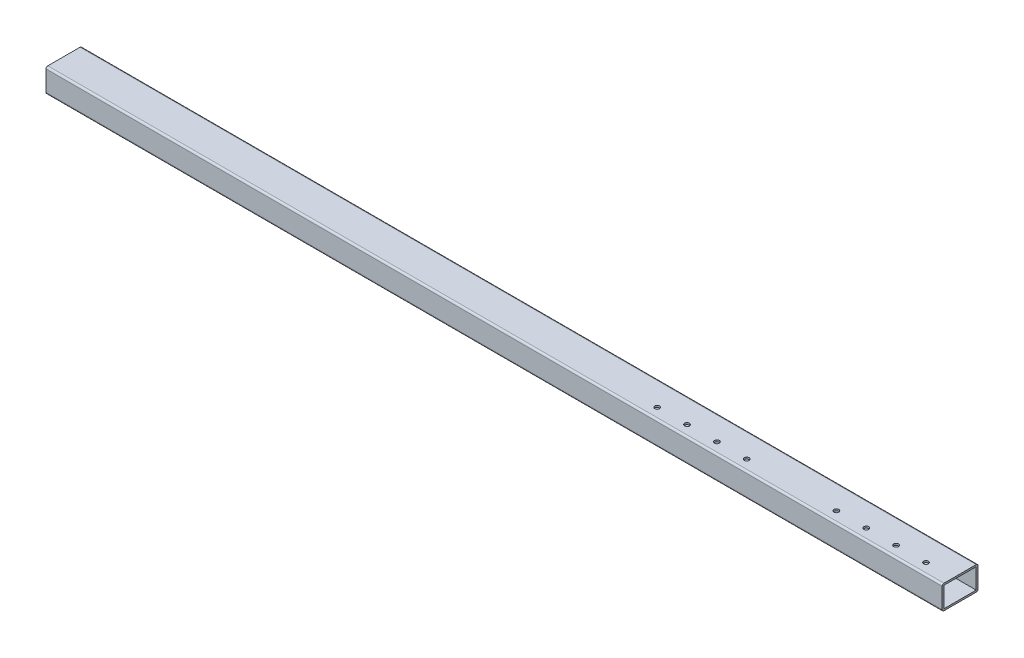
SolidWorks part; units mm, degrees
ref_plane "Спереди" through (0, 0, 0) normal (0, 0, 1) x (1, 0, 0)
ref_plane "Сверху" through (0, 0, 0) normal (0, 1, 0) x (1, 0, 0)
ref_plane "Справа" through (0, 0, 0) normal (1, 0, 0) x (0, 0, -1)
sketch "Эскиз1" plane through (0, 0, 0) normal (1, 0, 0) x (0, 0, -1)
  line L1 (-27, 20) -> (27, 20)
  line L2 (-30, 17) -> (-30, -17)
  line L3 (-27, -20) -> (27, -20)
  line L4 (30, 17) -> (30, -17)
  line L5 (-30, 20) -> (30, -20) construction
  line L6 (-30, -20) -> (30, 20) construction
  arc A0 (-27, 20) -> (-30, 17) centre (-27, 17) ccw
  arc A1 (-30, -17) -> (-27, -20) centre (-27, -17) ccw
  arc A2 (27, -20) -> (30, -17) centre (27, -17) ccw
  arc A3 (27, 20) -> (30, 17) centre (27, 17) cw
  point P0 (0, 0)
  dimension "D1" = 3
extrude "Вытянуть-Тонкостенный1" add sketch "Эскиз1" along normal blind 1500 thin
sketch "Эскиз2" plane through (0, 20, 0) normal (0, 1, 0) x (1, 0, 0)
  circle A0 centre (1455, -12) radius 4.05
  circle A1 centre (1405, -12) radius 4.05
  circle A2 centre (1355, -12) radius 4.05
  circle A3 centre (1305, -12) radius 4.05
  circle A4 centre (1155, -12) radius 4.05
  circle A5 centre (1105, -12) radius 4.05
  circle A6 centre (1055, -12) radius 4.05
  circle A7 centre (1005, -12) radius 4.05
  dimension "D1" = 4
  dimension "D2" = 2
extrude "Вырез-Вытянуть1" cut sketch "Эскиз2" against normal through all
